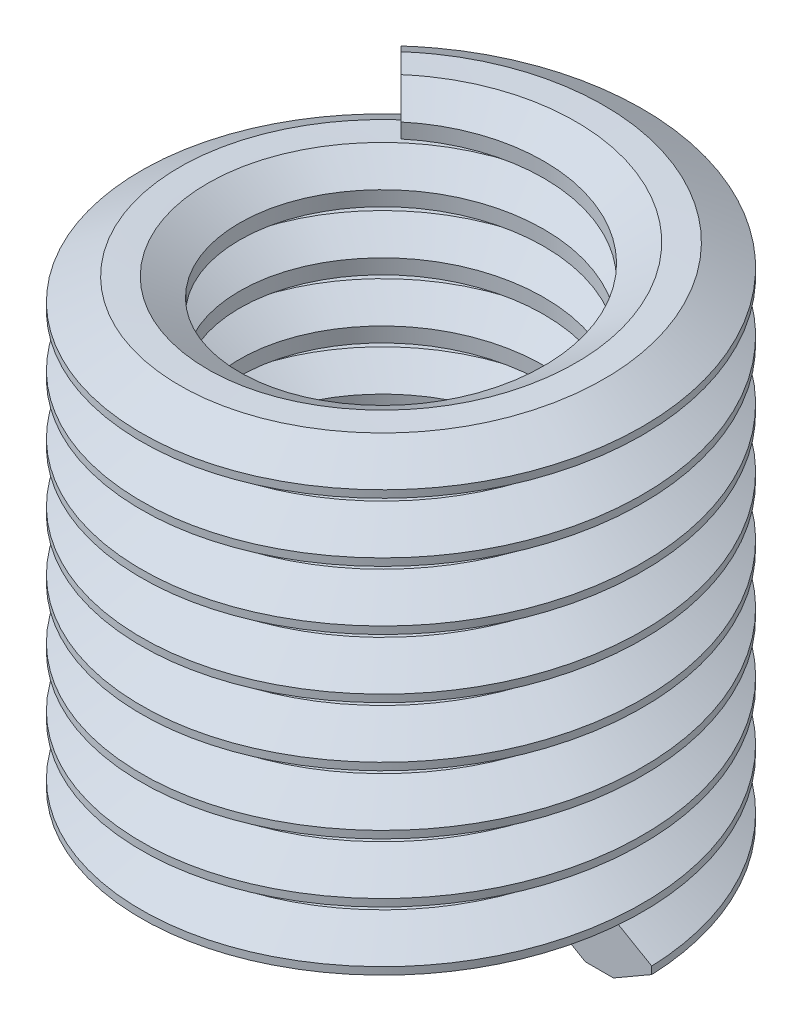
SolidWorks part; units mm, degrees
ref_plane "Front Plane" through (0, 0, 0) normal (0, 0, 1) x (1, 0, 0)
ref_plane "Top Plane" through (0, 0, 0) normal (0, 1, 0) x (1, 0, 0)
ref_plane "Right Plane" through (0, 0, 0) normal (1, 0, 0) x (0, 0, -1)
sketch "Sketch1" plane through (0, 0, 0) normal (0, 0, 1) x (-1, 0, 0)
  line L0 (0, 0) -> (0, 9.525) construction
  line L1 (-1.8938, 0) -> (-2.5866, 0.4) construction
  line L2 (-2.7938, 0.4) -> (-3.4866, 0) construction
  line L3 (-3.4866, 0) -> (-2.7938, -0.4) construction
  line L4 (-2.5866, -0.4) -> (-1.8938, 0) construction
  line L5 (-2.5866, -0.4) -> (-2.5866, 0.4) construction
  line L6 (-1.8938, 0) -> (0, 0) construction
  line L8 (-3.4, -0.05) -> (-2.8804, -0.35)
  line L9 (-2.5, -0.35) -> (-2.067, -0.1)
  line L10 (-1.9804, -0.05) -> (-1.9804, 0.05) construction
  line L11 (-2.067, 0.1) -> (-2.5, 0.35)
  line L12 (-2.8804, 0.35) -> (-3.4, 0.05)
  line L13 (-1.8938, 0) -> (-1.9804, 0) construction
  line L14 (-1.9804, 0) -> (-2.5, 0) construction
  line L15 (-2.8804, 0) -> (-3.4, 0) construction
  line L16 (-3.4, 0) -> (-3.4866, 0) construction
  line L17 (-2.8804, 0.35) -> (-2.5, 0.35)
  line L18 (-2.5, 0.35) -> (-2.5, -0.35) construction
  line L19 (-2.5, -0.35) -> (-2.8804, -0.35)
  line L20 (-2.8804, -0.35) -> (-2.8804, 0.35) construction
  line L21 (-2.8804, 0) -> (-2.5866, 0) construction
  line L22 (-2.5866, 0) -> (-2.5, 0) construction
  line L23 (-3.4, 0.4) -> (-3.4, -7.1) construction
  line L24 (-2.067, -0.1) -> (-2.067, 0.1)
  line L25 (-2.067, 0) -> (-1.9804, 0) construction
  line L26 (-3.4, -0.05) -> (-3.4, 0.05)
  line L28 (3.4, 0.4) -> (3.4, -7.1) construction
  line L29 (-2.5866, -0.4) -> (-2.7938, -0.4) construction
  line L31 (-2.7938, 0.4) -> (-2.5866, 0.4) construction
  dimension "D3" = 0.8
  dimension "D4" = 0.1
  dimension "Installed Length" = 7.5
  dimension "Thread Size" = 5
  dimension "Max OD" = 6.8
sketch "Sketch2" plane through (0, 0, 0) normal (0, 1, 0) x (1, 0, 0)
  circle A0 centre (0, 0) radius 2.5
curve "Helix/Spiral1" pitch 0.8 height 6.7 turns 8.375 parameters "Height"=6.7, "Pitch"=0.8
sweep "Sweep1" add profiles "Sketch1" path "Helix/Spiral1"
equation "\"D3@Sketch1\" = \"Pitch@Helix/Spiral1\""
equation "\"D4@Sketch1\" = \"D3@Sketch1\"  * 1 / 8"
equation "\"Height@Helix/Spiral1\" = \"Installed Length@Sketch1\" - \"Pitch@Helix/Spiral1\""
